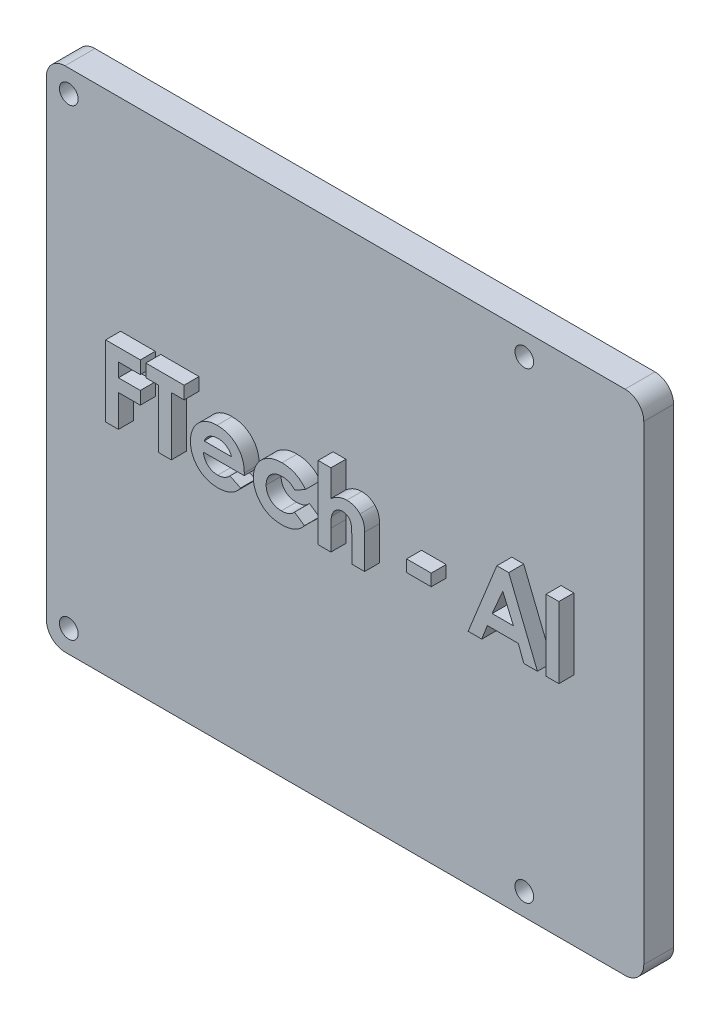
SolidWorks part; units mm, degrees
ref_plane "Front Plane" through (0, 0, 0) normal (0, 0, 1) x (1, 0, 0)
ref_plane "Top Plane" through (0, 0, 0) normal (0, 1, 0) x (1, 0, 0)
ref_plane "Right Plane" through (0, 0, 0) normal (1, 0, 0) x (0, 0, -1)
sketch "Sketch1" plane through (0, 0, 0) normal (0, 0, 1) x (1, 0, 0)
  line L1 (0, 0) -> (80, 0)
  line L2 (0, 0) -> (0, -68)
  line L3 (0, -68) -> (80, -68)
  line L4 (80, 0) -> (80, -68)
  dimension "D1" = 80
  dimension "D2" = 80
  dimension "D3" = 68
extrude "Boss-Extrude1" add sketch "Sketch1" along normal blind 4
sketch "Sketch2" plane through (0, 0, 4) normal (0, 0, 1) x (1, 0, 0)
  line L0 (0, 0) -> (0, -68) construction
  text T0 "<b>FTech - AI</b>\r\n" font "Century Gothic" height in points 36
extrude "Boss-Extrude2" add sketch "Sketch2" along normal blind 2
sketch "Sketch3" plane through (0, 0, 4) normal (0, 0, 1) x (1, 0, 0)
  line L0 (0, 0) -> (0, -68) construction
  line L1 (80, 0) -> (0, 0) construction
  line L2 (0, -68) -> (80, -68) construction
  line L3 (80, -68) -> (80, 0) construction
  circle A0 centre (3, -3) radius 1.25
  circle A1 centre (3, -65) radius 1.25
  circle A2 centre (64, -65) radius 1.25
  circle A3 centre (64, -3) radius 1.25
  point P8 (4.146, -19.9793)
  point P9 (3, -64.6221)
  point P14 (44.8417, -65)
  point P19 (64, -3)
  dimension "D1" = 3
  dimension "D2" = 3
  dimension "D3" = 2.5
  dimension "D4" = 3
  dimension "D5" = 2.5
  dimension "D6" = 3
  dimension "D7" = 16
  dimension "D8" = 3
  dimension "D9" = 3
  dimension "D10" = 16
extrude "Cut-Extrude1" cut sketch "Sketch3" against normal blind 10
fillet "Fillet1" radius 2.5 4 edges at (0, -68, 2) (0, 0, 2) (80, 0, 2) (80, -68, 2)
